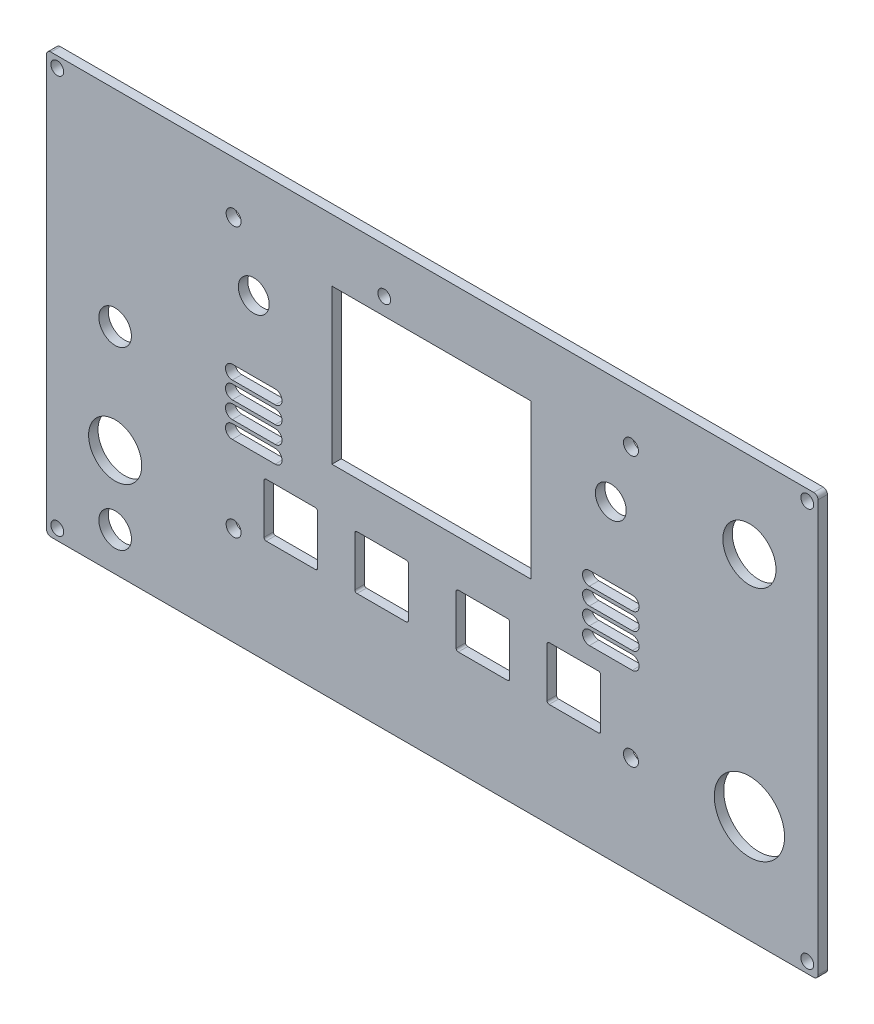
SolidWorks part; units mm, degrees
ref_plane "Спереди" through (0, 0, 0) normal (0, 0, 1) x (1, 0, 0)
ref_plane "Сверху" through (0, 0, 0) normal (0, 1, 0) x (1, 0, 0)
ref_plane "Справа" through (0, 0, 0) normal (1, 0, 0) x (0, 0, -1)
sketch "Эскиз1" plane through (0, 0, 0) normal (0, 0, 1) x (1, 0, 0)
  line L0 (3.556, 69.977) -> (3.556, 0) construction
  line L1 (0, 0) -> (99.822, 0) construction
  line L2 (0, 0) -> (0, 69.977) construction
  line L3 (0, 69.977) -> (99.822, 69.977) construction
  line L4 (99.822, 0) -> (99.822, 69.977) construction
  line L5 (96.266, 69.977) -> (96.266, 0) construction
  line L6 (0, 66.421) -> (99.822, 66.421) construction
  line L7 (0, 3.556) -> (99.822, 3.556) construction
  line L8 (49.911, 69.977) -> (49.911, 0) construction
  line L9 (0, 34.9885) -> (99.822, 34.9885) construction
  line L10 (-40.089, 5.5) -> (139.911, 5.5) construction
  line L11 (-40.089, 78.5) -> (139.911, 78.5)
  line L12 (-40.089, 78.5) -> (-40.089, -19.5)
  line L13 (-40.089, -19.5) -> (139.911, -19.5)
  line L14 (139.911, 78.5) -> (139.911, -19.5)
  line L15 (-40.089, 78.5) -> (139.911, -19.5) construction
  line L16 (-40.089, -19.5) -> (139.911, 78.5) construction
  line L17 (-40.089, 58.5) -> (139.911, 58.5) construction
  line L18 (-24.089, 78.5) -> (-24.089, -19.5) construction
  line L19 (123.911, 78.5) -> (123.911, -19.5) construction
  line L20 (-37.589, 78.5) -> (-37.589, -20.4429) construction
  line L21 (137.411, 78.5) -> (137.411, -19.5) construction
  line L22 (-40.089, 76) -> (139.911, 76) construction
  line L23 (-40.089, -17) -> (139.911, -17) construction
  line L24 (0, 52.959) -> (99.822, 52.959) construction
  line L25 (0, 11.049) -> (99.822, 11.049) construction
  line L26 (8.255, 69.977) -> (8.255, 0) construction
  line L27 (91.567, 69.977) -> (91.567, 0) construction
  line L28 (16.891, 0) -> (16.891, 11.049) construction
  line L29 (38.1, 0) -> (38.1, 11.049) construction
  line L30 (61.722, 0) -> (61.722, 11.049) construction
  line L31 (82.931, 0) -> (82.931, 11.049) construction
  line L32 (3.255, 34.9885) -> (13.255, 34.9885) construction
  line L33 (10.641, 17.299) -> (23.141, 17.299)
  line L34 (10.641, 17.299) -> (10.641, 4.799)
  line L35 (10.641, 4.799) -> (23.141, 4.799)
  line L36 (23.141, 17.299) -> (23.141, 4.799)
  line L37 (10.641, 17.299) -> (23.141, 4.799) construction
  line L38 (10.641, 4.799) -> (23.141, 17.299) construction
  line L39 (31.85, 17.299) -> (44.35, 17.299)
  line L40 (31.85, 17.299) -> (31.85, 4.799)
  line L41 (31.85, 4.799) -> (44.35, 4.799)
  line L42 (44.35, 17.299) -> (44.35, 4.799)
  line L43 (31.85, 17.299) -> (44.35, 4.799) construction
  line L44 (31.85, 4.799) -> (44.35, 17.299) construction
  line L45 (55.472, 17.299) -> (67.972, 17.299)
  line L46 (55.472, 17.299) -> (55.472, 4.799)
  line L47 (55.472, 4.799) -> (67.972, 4.799)
  line L48 (67.972, 17.299) -> (67.972, 4.799)
  line L49 (55.472, 17.299) -> (67.972, 4.799) construction
  line L50 (55.472, 4.799) -> (67.972, 17.299) construction
  line L51 (76.681, 17.299) -> (89.181, 17.299)
  line L52 (76.681, 17.299) -> (76.681, 4.799)
  line L53 (76.681, 4.799) -> (89.181, 4.799)
  line L54 (89.181, 17.299) -> (89.181, 4.799)
  line L55 (76.681, 17.299) -> (89.181, 4.799) construction
  line L56 (76.681, 4.799) -> (89.181, 17.299) construction
  line L57 (26.5, 28) -> (73, 28)
  line L58 (26.5, 28) -> (26.5, 64)
  line L59 (26.5, 64) -> (73, 64)
  line L60 (73, 28) -> (73, 64)
  line L61 (3.255, 36.5885) -> (13.255, 36.5885)
  line L62 (3.255, 33.3885) -> (13.255, 33.3885)
  line L63 (96.567, 34.9885) -> (86.567, 34.9885) construction
  line L64 (96.567, 33.3885) -> (86.567, 33.3885)
  line L65 (96.567, 36.5885) -> (86.567, 36.5885)
  line L66 (3.255, 30.9885) -> (13.255, 30.9885) construction
  line L67 (3.255, 32.5885) -> (13.255, 32.5885)
  line L68 (3.255, 29.3885) -> (13.255, 29.3885)
  line L69 (96.567, 30.9885) -> (86.567, 30.9885) construction
  line L70 (96.567, 29.3885) -> (86.567, 29.3885)
  line L71 (96.567, 32.5885) -> (86.567, 32.5885)
  line L72 (3.255, 26.9885) -> (13.255, 26.9885) construction
  line L73 (3.255, 28.5885) -> (13.255, 28.5885)
  line L74 (3.255, 25.3885) -> (13.255, 25.3885)
  line L75 (96.567, 26.9885) -> (86.567, 26.9885) construction
  line L76 (96.567, 25.3885) -> (86.567, 25.3885)
  line L77 (96.567, 28.5885) -> (86.567, 28.5885)
  line L78 (3.255, 22.9885) -> (13.255, 22.9885) construction
  line L79 (3.255, 24.5885) -> (13.255, 24.5885)
  line L80 (3.255, 21.3885) -> (13.255, 21.3885)
  line L81 (96.567, 22.9885) -> (86.567, 22.9885) construction
  line L82 (96.567, 21.3885) -> (86.567, 21.3885)
  line L83 (96.567, 24.5885) -> (86.567, 24.5885)
  circle A0 centre (-24.089, 5.5) radius 6.2
  circle A2 centre (123.911, 58.5) radius 6.2
  circle A3 centre (123.911, 5.5) radius 8.2
  circle A4 centre (-37.589, 76) radius 1.5
  circle A5 centre (137.411, 76) radius 1.5
  circle A6 centre (137.411, -17) radius 1.5
  circle A7 centre (-37.589, -17) radius 1.5
  circle A8 centre (3.556, 3.556) radius 1.75
  circle A9 centre (3.556, 66.421) radius 1.75
  circle A10 centre (96.266, 66.421) radius 1.75
  circle A11 centre (96.266, 3.556) radius 1.75
  circle A12 centre (8.255, 52.959) radius 3.6
  circle A13 centre (91.567, 52.959) radius 3.6
  circle A14 centre (-24.089, 30.5) radius 3.8
  circle A15 centre (-24.089, -10.5) radius 3.8
  arc A16 (3.255, 36.5885) -> (3.255, 33.3885) centre (3.255, 34.9885) ccw
  arc A17 (13.255, 33.3885) -> (13.255, 36.5885) centre (13.255, 34.9885) ccw
  arc A18 (96.567, 33.3885) -> (96.567, 36.5885) centre (96.567, 34.9885) ccw
  arc A19 (86.567, 36.5885) -> (86.567, 33.3885) centre (86.567, 34.9885) ccw
  arc A20 (3.255, 32.5885) -> (3.255, 29.3885) centre (3.255, 30.9885) ccw
  arc A21 (13.255, 29.3885) -> (13.255, 32.5885) centre (13.255, 30.9885) ccw
  arc A22 (96.567, 29.3885) -> (96.567, 32.5885) centre (96.567, 30.9885) ccw
  arc A23 (86.567, 32.5885) -> (86.567, 29.3885) centre (86.567, 30.9885) ccw
  arc A24 (3.255, 28.5885) -> (3.255, 25.3885) centre (3.255, 26.9885) ccw
  arc A25 (13.255, 25.3885) -> (13.255, 28.5885) centre (13.255, 26.9885) ccw
  arc A26 (96.567, 25.3885) -> (96.567, 28.5885) centre (96.567, 26.9885) ccw
  arc A27 (86.567, 28.5885) -> (86.567, 25.3885) centre (86.567, 26.9885) ccw
  arc A28 (3.255, 24.5885) -> (3.255, 21.3885) centre (3.255, 22.9885) ccw
  arc A29 (13.255, 21.3885) -> (13.255, 24.5885) centre (13.255, 22.9885) ccw
  arc A30 (96.567, 21.3885) -> (96.567, 24.5885) centre (96.567, 22.9885) ccw
  arc A31 (86.567, 24.5885) -> (86.567, 21.3885) centre (86.567, 22.9885) ccw
  circle A32 centre (38.7, 68) radius 1.5
  point P17 (49.911, 34.9885)
  point P105 (8.255, 34.9885)
  point P113 (91.567, 34.9885)
  point P120 (8.255, 30.9885)
  point P128 (91.567, 30.9885)
  point P134 (8.255, 26.9885)
  point P142 (91.567, 26.9885)
  point P148 (8.255, 22.9885)
  point P156 (91.567, 22.9885)
  dimension "D13" = 12.4
  dimension "D14" = 16.4
  dimension "D15" = 12.4
  dimension "D16" = 7.6
  dimension "D21" = 3
  dimension "D22" = 3
  dimension "D23" = 3
  dimension "D24" = 3
  dimension "D25" = 3.5
  dimension "D26" = 3.5
  dimension "D27" = 3.5
  dimension "D28" = 3.5
  dimension "D33" = 7.2
  dimension "D34" = 7.2
  dimension "D53" = 7.6
  dimension "D63" = 3
  dimension "D1" = 99.822
  dimension "D2" = 69.977
  dimension "D3" = 3.556
  dimension "D4" = 3.556
  dimension "D5" = 3.556
  dimension "D6" = 3.556
  dimension "D7" = 98
  dimension "D8" = 180
  dimension "D9" = 25
  dimension "D10" = 20
  dimension "D11" = 16
  dimension "D12" = 16
  dimension "D17" = 2.5
  dimension "D18" = 2.5
  dimension "D19" = 2.5
  dimension "D20" = 2.5
  dimension "D29" = 52.959
  dimension "D30" = 11.049
  dimension "D31" = 8.255
  dimension "D32" = 91.567
  dimension "D35" = 16.891
  dimension "D36" = 38.1
  dimension "D37" = 61.722
  dimension "D38" = 82.931
  dimension "D39" = 12.5
  dimension "D40" = 12.5
  dimension "D41" = 12.5
  dimension "D42" = 12.5
  dimension "D43" = 12.5
  dimension "D44" = 12.5
  dimension "D45" = 12.5
  dimension "D46" = 12.5
  dimension "D47" = 17
  dimension "D48" = 6.023
  dimension "D49" = 26.5
  dimension "D50" = 28
  dimension "D51" = 73
  dimension "D52" = 64
  dimension "D54" = 16
  dimension "D55" = 25
  dimension "D56" = 10
  dimension "D57" = 3.2
  dimension "D58" = 10
  dimension "D59" = 3.2
  dimension "D61" = 38.7
  dimension "D62" = 68
  dimension "D64" = 0
  dimension "D60" = 4
extrude "Бобышка-Вытянуть1" add sketch "Эскиз1" along normal blind 2.2
fillet "Скругление1" radius 1 4 edges at (139.911, -19.5, 1.1) (-40.089, -19.5, 1.1) (-40.089, 78.5, 1.1) (139.911, 78.5, 1.1)
fillet "Скругление2" radius 0.5 16 edges at (89.181, 4.799, 1.1) (89.181, 17.299, 1.1) (76.681, 17.299, 1.1) (76.681, 4.799, 1.1) (67.972, 4.799, 1.1) (67.972, 17.299, 1.1) (55.472, 17.299, 1.1) (55.472, 4.799, 1.1) (44.35, 4.799, 1.1) (44.35, 17.299, 1.1) (31.85, 17.299, 1.1) (31.85, 4.799, 1.1) (10.641, 4.799, 1.1) (23.141, 4.799, 1.1) (23.141, 17.299, 1.1) (10.641, 17.299, 1.1)
